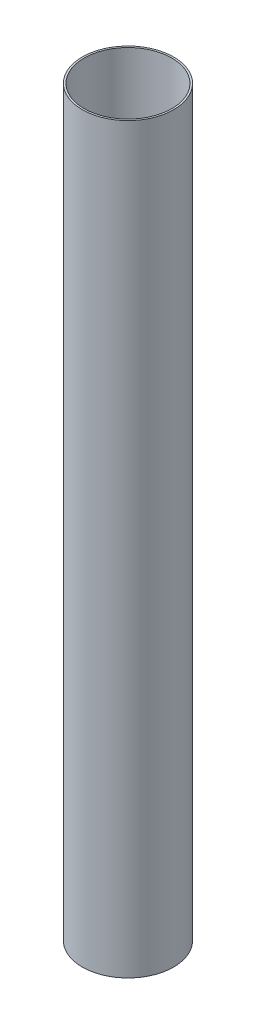
SolidWorks part; units mm, degrees
ref_plane "Front Plane" through (0, 0, 0) normal (0, 0, 1) x (1, 0, 0)
ref_plane "Top Plane" through (0, 0, 0) normal (0, 1, 0) x (1, 0, 0)
ref_plane "Right Plane" through (0, 0, 0) normal (1, 0, 0) x (0, 0, -1)
sketch "Sketch1" plane through (0, 0, 0) normal (0, 0, 1) x (1, 0, 0)
  line L0 (49.53, 0) -> (51.5874, 0)
  line L1 (51.5874, 0) -> (51.5874, 838.2)
  line L2 (51.5874, 838.2) -> (49.53, 838.2)
  line L7 (49.53, 0) -> (49.53, 838.2)
  dimension "D1" = 49.53
  dimension "D2" = 2.0574
  dimension "D3" = 838.2
  dimension "D4" = 0
ref_axis "Central Axis" through (0, 123.6201, 0) along (0, -1, 0)
revolve "Revolve1" add sketch "Sketch1" angle 360 about axis through (0, 123.6201, 0) along (0, -1, 0)
